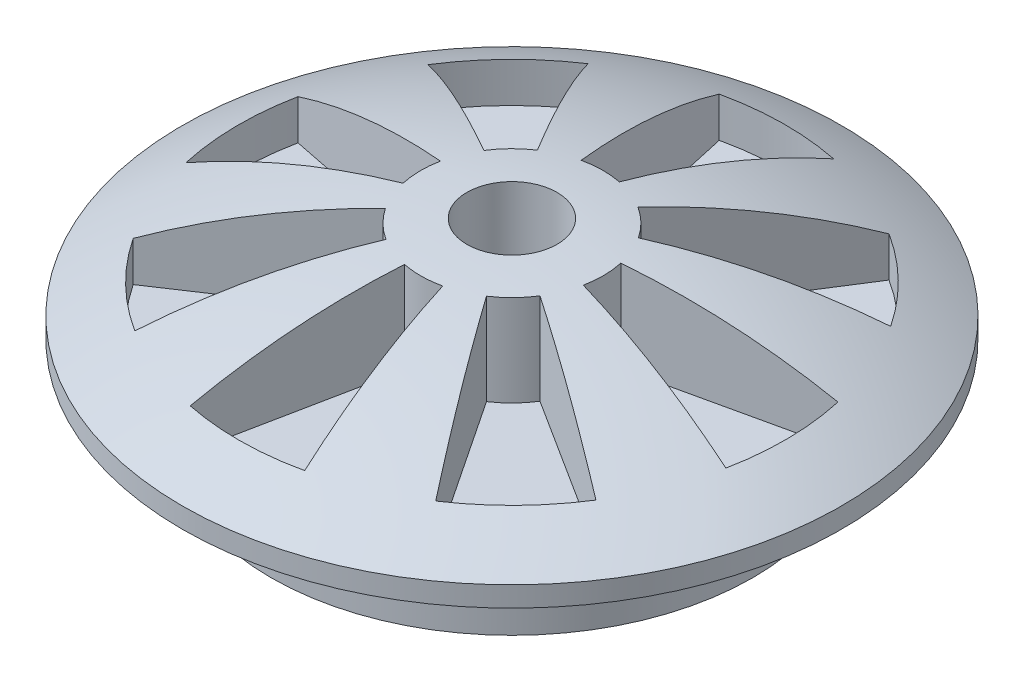
SolidWorks part; units mm, degrees
ref_plane "Front Plane" through (0, 0, 0) normal (0, 0, 1) x (1, 0, 0)
ref_plane "Top Plane" through (0, 0, 0) normal (0, 1, 0) x (1, 0, 0)
ref_plane "Right Plane" through (0, 0, 0) normal (1, 0, 0) x (0, 0, -1)
sketch "Sketch1" plane through (0, 0, 0) normal (0, 0, 1) x (1, 0, 0)
  line L0 (95.7246, 0) -> (-99.9885, 0) construction
  line L1 (0, 46.3699) -> (0, -58.522) construction
  line L2 (-92.075, 0) -> (-92.075, -5.6497)
  line L3 (-92.075, -5.6497) -> (-67.31, -5.6497)
  line L4 (-67.31, -5.6497) -> (-67.31, -29.7407)
  line L5 (-67.31, -29.7407) -> (0, -29.7407)
  line L6 (0, -29.7407) -> (0, 0)
  line L7 (0, 0) -> (0, 23.7712)
  arc A0 (-92.075, 0) -> (0, 23.7712) centre (-3.2104, -153.9998) cw
  dimension "D2" = 177.8
  dimension "D3" = 67.31
  dimension "D1" = 92.075
revolve "Revolve1" add sketch "Sketch1" angle 360 about L1
sketch "Sketch4" plane through (0, -5.6497, 0) normal (0, -1, 0) x (1, 0, 0)
  line L0 (24.9878, 5.0284) -> (74.8228, 15.0571)
  line L1 (24.8787, -5.5427) -> (74.4964, -16.597)
  circle A0 centre (0, 0) radius 76.3228 construction
  circle A1 centre (0, 0) radius 25.4887 construction
  arc A2 (74.4964, -16.597) -> (74.8228, 15.0571) centre (0, 0) ccw
  arc A3 (24.9878, 5.0284) -> (24.8787, -5.5427) centre (0, 0) cw
extrude "Cut-Extrude3" cut sketch "Sketch4" against normal up to next from offset 2.54
pattern_circular "CirPattern2" count 8 over 360 about axis through (0, 0, 0) along (0, 1, 0) of "Cut-Extrude3"
sketch "Sketch6" plane through (0, -5.6497, 0) normal (0, -1, 0) x (1, 0, 0)
  circle A0 centre (0, 0) radius 12.5921
extrude "Cut-Extrude4" cut sketch "Sketch6" against normal up to next
scale "Scale1" scale about centroid uniform scaling yes scale factor 0.965517
